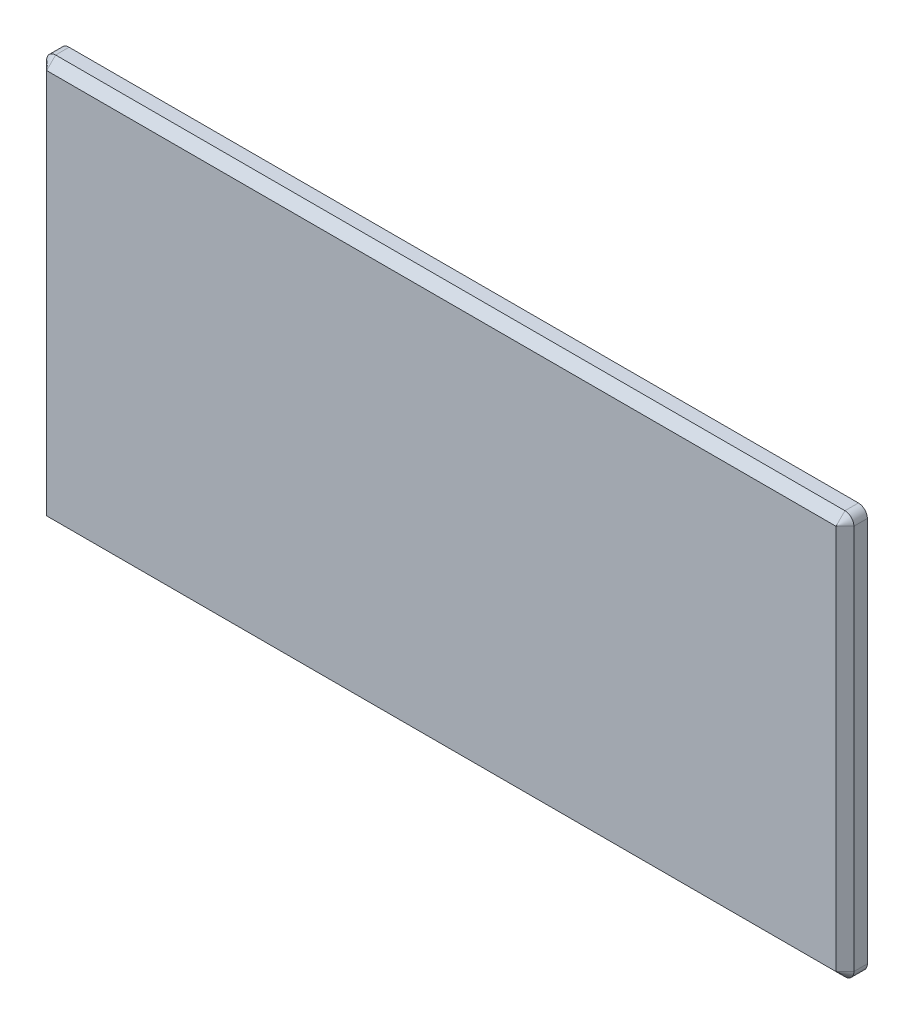
SolidWorks part; units mm, degrees
material "POM Acetal Copolymer"
ref_plane "Plan de face" through (0, 0, 0) normal (0, 0, 1) x (1, 0, 0)
ref_plane "Plan de dessus" through (0, 0, 0) normal (0, 1, 0) x (1, 0, 0)
ref_plane "Plan de droite" through (0, 0, 0) normal (1, 0, 0) x (0, 0, -1)
sketch "Sketch1" plane through (0, 0, 0) normal (0, 0, 1) x (1, 0, 0)
  line L1 (-45, -22.5) -> (45, -22.5)
  line L2 (-45, -22.5) -> (-45, 22.5)
  line L3 (-45, 22.5) -> (45, 22.5)
  line L4 (45, -22.5) -> (45, 22.5)
  line L5 (-45, -22.5) -> (45, 22.5) construction
  line L6 (-45, 22.5) -> (45, -22.5) construction
  point P0 (0, 0)
  dimension "D1" = 45
  dimension "D2" = 90
extrude "Boss-Extrude1" add sketch "Sketch1" along normal blind 2.5
fillet "Fillet1" radius 1 4 edges at (-45, -22.5, 1.25) (-45, 22.5, 1.25) (45, 22.5, 1.25) (45, -22.5, 1.25)
chamfer "Chamfer1" distance 1 angle 45 8 edges at (0, -22.5, 2.5) (-45, 0, 2.5) (0, 22.5, 2.5) (45, 0, 2.5) (-44.7071, 22.2071, 2.5) (44.7071, 22.2071, 2.5) (44.7071, -22.2071, 2.5) (-44.7071, -22.2071, 2.5)
sketch "Sketch2" plane through (0, 0, 0) normal (0, 0, -1) x (-1, 0, 0)
  circle A0 centre (-22.5, 0) radius 4
  circle A1 centre (22.5, 0) radius 4
  dimension "D1" = 45
  dimension "D3" = 8
  dimension "D2" = 22.5
extrude "Boss-Extrude2" add sketch "Sketch2" along normal blind 10
